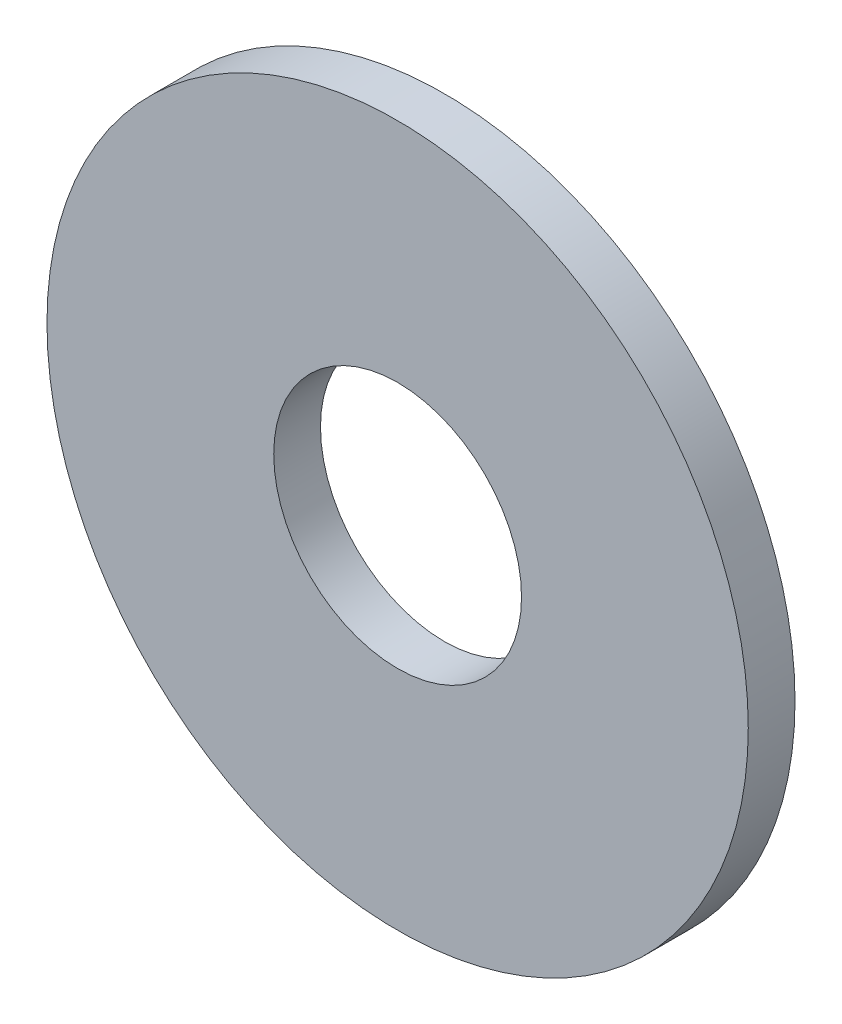
SolidWorks part; units mm, degrees
ref_plane "Front Plane" through (0, 0, 0) normal (0, 0, 1) x (1, 0, 0)
ref_plane "Top Plane" through (0, 0, 0) normal (0, 1, 0) x (1, 0, 0)
ref_plane "Right Plane" through (0, 0, 0) normal (1, 0, 0) x (0, 0, -1)
sketch "Sketch1" plane through (0, 0, 0) normal (0, 0, 1) x (1, 0, 0)
  circle A0 centre (0, 0) radius 2.65
  circle A1 centre (0, 0) radius 7.5
  dimension "ID" = 5.3
  dimension "OD" = 15
extrude "Extrude1" add sketch "Sketch1" against normal blind 1
